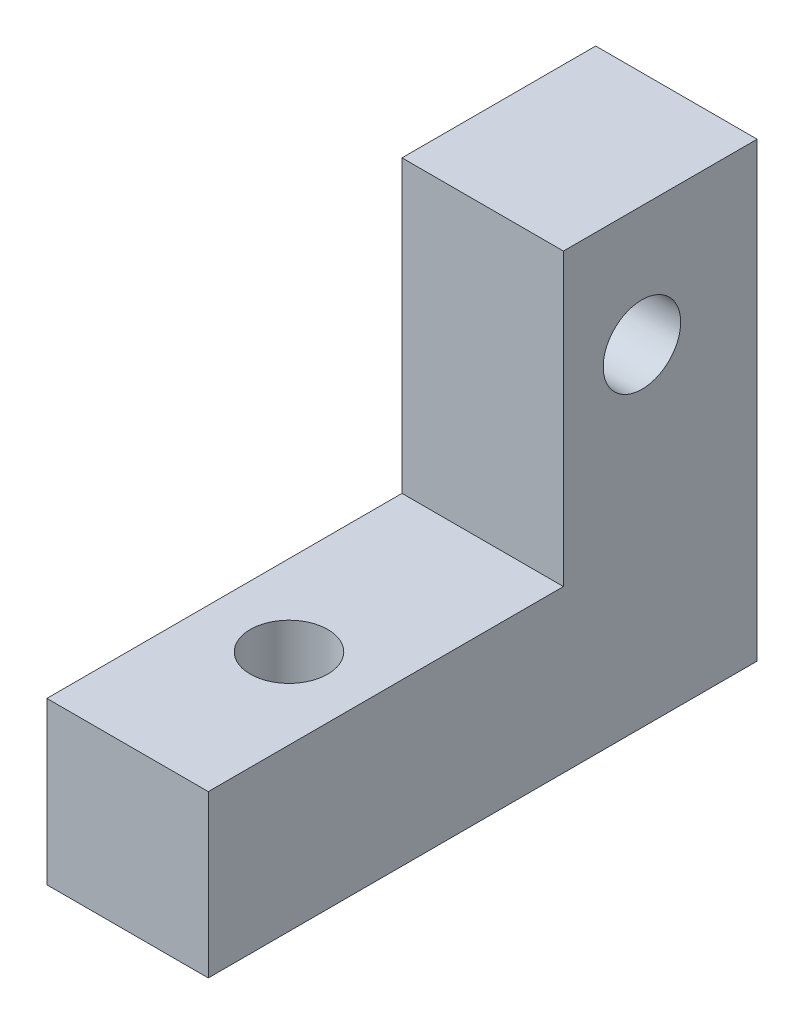
SolidWorks part; units mm, degrees
ref_plane "Front Plane" through (0, 0, 0) normal (0, 0, 1) x (1, 0, 0)
ref_plane "Top Plane" through (0, 0, 0) normal (0, 1, 0) x (1, 0, 0)
ref_plane "Right Plane" through (0, 0, 0) normal (1, 0, 0) x (0, 0, -1)
sketch "Sketch3" plane through (0, 0, 0) normal (1, 0, 0) x (0, 0, -1)
  line L0 (0, 0) -> (0, 6.35)
  line L1 (0, 6.35) -> (13.97, 6.35)
  line L2 (0, 0) -> (21.59, 0)
  line L3 (21.59, 0) -> (21.59, 17.78)
  line L4 (21.59, 17.78) -> (13.97, 17.78)
  line L5 (13.97, 17.78) -> (13.97, 6.35)
  dimension "D1" = 13.97
  dimension "D2" = 6.35
  dimension "D3" = 21.59
  dimension "D4" = 17.78
  dimension "D5" = 7.62
extrude "Boss-Extrude1" add sketch "Sketch3" along normal blind 6.35
sketch "Sketch4" plane through (0, 6.35, 0) normal (0, 1, 0) x (1, 0, 0)
  line L0 (3.175, 0) -> (3.175, 6.35)
  line L1 (6.35, 0) -> (0, 0) construction
  circle A0 centre (3.175, 6.35) radius 1.524
  dimension "D1" = 6.35
extrude "Cut-Extrude1" cut sketch "Sketch4" against normal blind 6.35
sketch "Sketch5" plane through (6.35, 0, 0) normal (1, 0, 0) x (0, 0, -1)
  line L1 (0, 0) -> (17.0576, 0)
  line L2 (0, 0) -> (21.59, 0) construction
  line L3 (17.0576, 0) -> (17.0576, 13.0516)
  circle A2 centre (17.0576, 13.0516) radius 1.524
  dimension "D1" = 13.0516
  dimension "D3" = 3.048
  dimension "D2" = 17.0576
extrude "Cut-Extrude3" cut sketch "Sketch5" against normal through all
